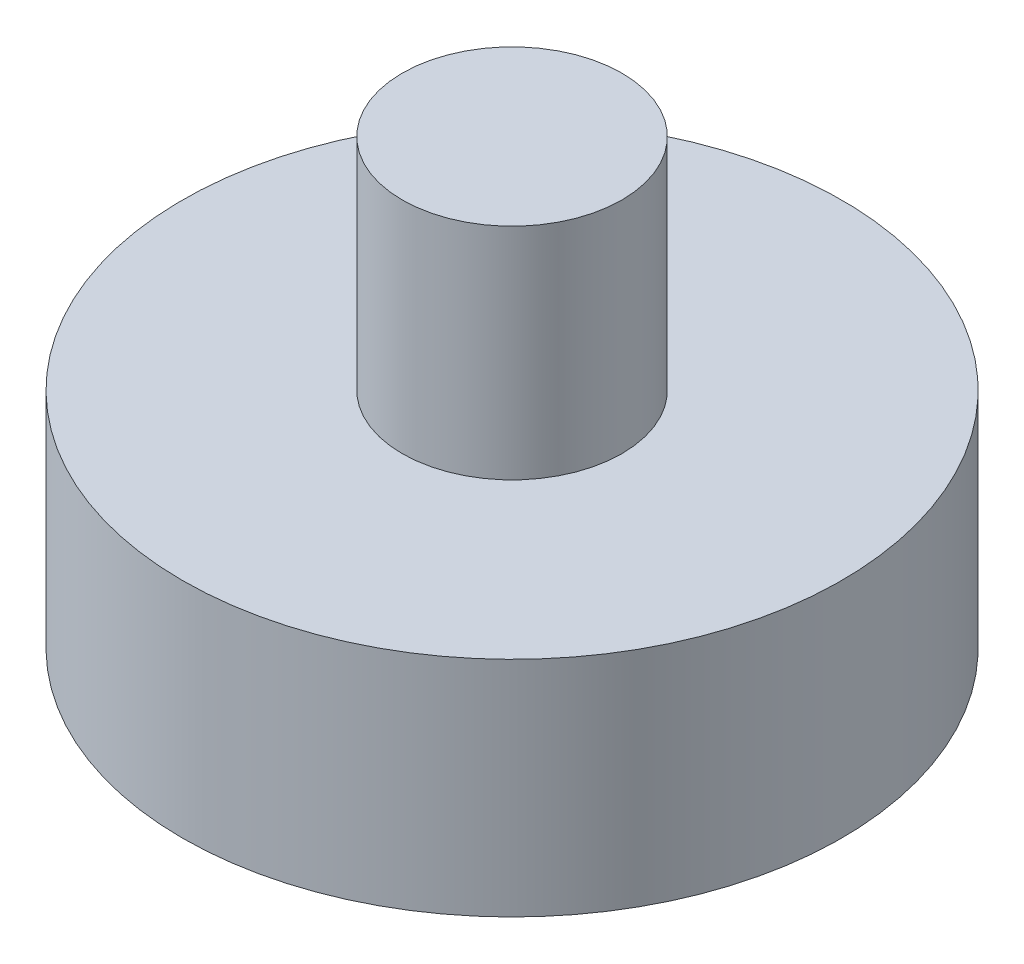
SolidWorks part; units mm, degrees
ref_plane "Front Plane" through (0, 0, 0) normal (0, 0, 1) x (1, 0, 0)
ref_plane "Top Plane" through (0, 0, 0) normal (0, 1, 0) x (1, 0, 0)
ref_plane "Right Plane" through (0, 0, 0) normal (1, 0, 0) x (0, 0, -1)
sketch "sketch1_link0" plane through (0, 0, 0) normal (0, 1, 0) x (1, 0, 0)
  circle A0 centre (0, 0) radius 60
  dimension "D1" = 120
extrude "Boss-Extrude1" add sketch "sketch1_link0" along normal mid plane 40.625
sketch "sketch2_link0" plane through (0, 20.3125, 0) normal (0, 1, 0) x (1, 0, 0)
  circle A0 centre (0, 0) radius 20
  dimension "D1" = 40
extrude "Boss-Extrude2" add sketch "sketch2_link0" along normal blind 40
equation "\"D1@Boss-Extrude1\"=0.1625*0.25m"
